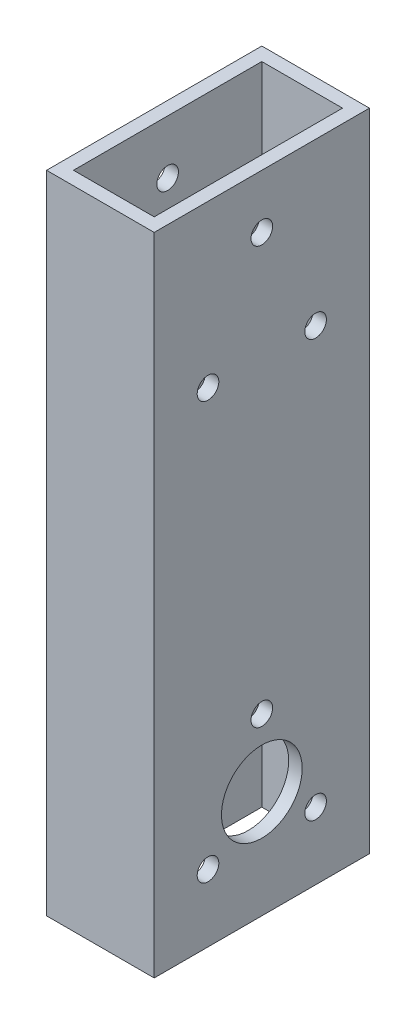
SolidWorks part; units mm, degrees
ref_plane "Front Plane" through (0, 0, 0) normal (0, 0, 1) x (1, 0, 0)
ref_plane "Top Plane" through (0, 0, 0) normal (0, 1, 0) x (1, 0, 0)
ref_plane "Right Plane" through (0, 0, 0) normal (1, 0, 0) x (0, 0, -1)
sketch "Sketch1" plane through (0, 0, 0) normal (0, 1, 0) x (1, 0, 0)
  line L1 (0, 0) -> (25.4, 0)
  line L2 (0, 0) -> (0, 50.8)
  line L3 (0, 50.8) -> (25.4, 50.8)
  line L4 (25.4, 0) -> (25.4, 50.8)
  line L5 (3.175, 3.175) -> (22.225, 3.175)
  line L6 (3.175, 3.175) -> (3.175, 47.625)
  line L7 (3.175, 47.625) -> (22.225, 47.625)
  line L8 (22.225, 3.175) -> (22.225, 47.625)
  dimension "D1" = 3.175
  dimension "D2" = 3.175
  dimension "D3" = 3.175
  dimension "D4" = 3.175
  dimension "D5" = 50.8
  dimension "D6" = 25.4
extrude "Boss-Extrude1" add sketch "Sketch1" along normal blind 152.4
sketch "Sketch2" plane through (25.4, 0, 0) normal (1, 0, 0) x (0, 0, -1)
  line L0 (12.7, 114.3) -> (38.1, 114.3) construction
  line L1 (0, 152.4) -> (50.8, 152.4) construction
  line L2 (0, 0) -> (50.8, 0) construction
  line L3 (12.7, 15.875) -> (38.1, 15.875) construction
  circle A0 centre (25.4, 139.7) radius 2.5527
  circle A1 centre (12.7, 114.3) radius 2.5527
  circle A2 centre (38.1, 114.3) radius 2.5527
  circle A3 centre (25.4, 41.275) radius 2.5527
  circle A4 centre (12.7, 15.875) radius 2.5527
  circle A5 centre (38.1, 15.875) radius 2.5527
  point P6 (25.4, 114.3)
  point P17 (25.4, 0)
  point P18 (25.4, 15.875)
  point P19 (25.4, 152.4)
  dimension "D4" = 5.1054
  dimension "D1" = 25.4
  dimension "D2" = 12.7
  dimension "D3" = 38.1
  dimension "D5" = 41.275
  dimension "D6" = 15.875
  dimension "D7" = 25.4
extrude "Cut-Extrude1" cut sketch "Sketch2" against normal blind 50.8
sketch "Sketch3" plane through (25.4, 0, 0) normal (1, 0, 0) x (0, 0, -1)
  line L0 (0, 0) -> (50.8, 0) construction
  circle A0 centre (25.4, 25.4) radius 9.525
  point P4 (25.4, 0)
  dimension "D1" = 19.05
  dimension "D2" = 25.4
extrude "Cut-Extrude2" cut sketch "Sketch3" against normal blind 25.4
